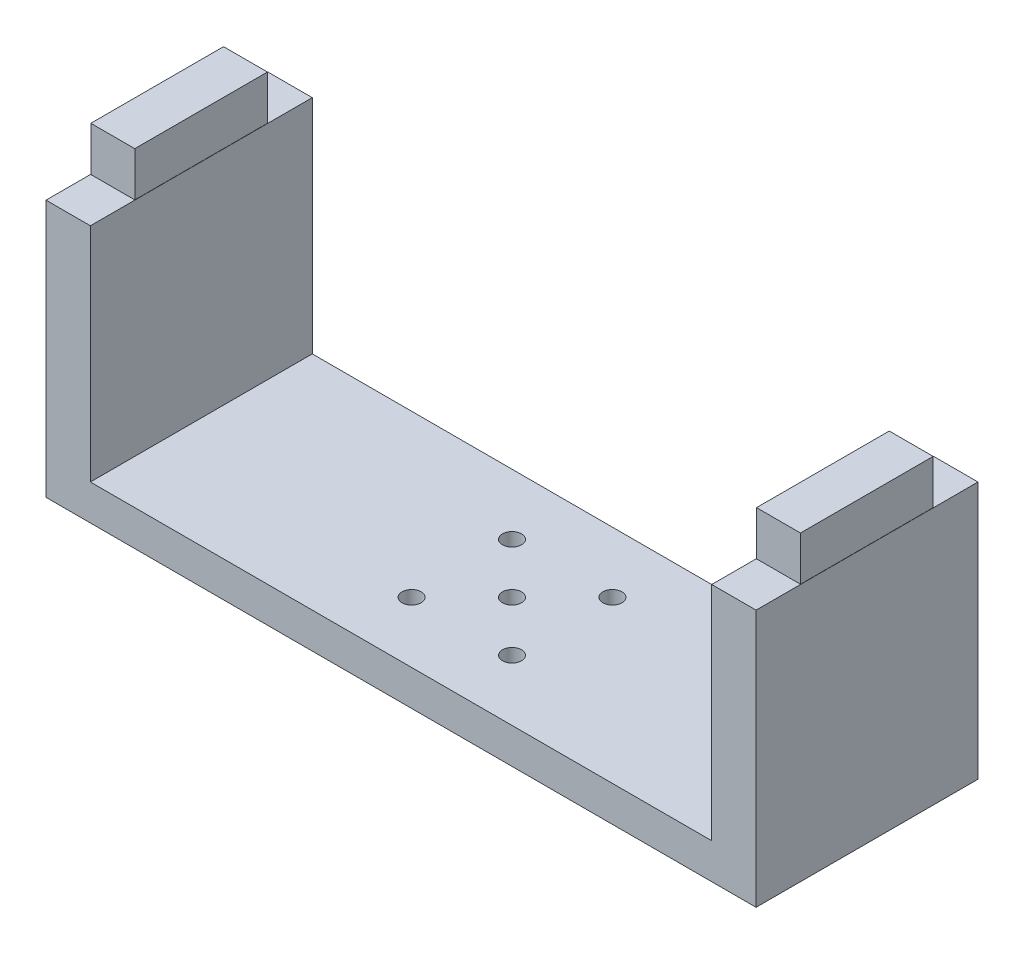
SolidWorks part; units mm, degrees
ref_plane "Front Plane" through (0, 0, 0) normal (0, 0, 1) x (1, 0, 0)
ref_plane "Top Plane" through (0, 0, 0) normal (0, 1, 0) x (1, 0, 0)
ref_plane "Right Plane" through (0, 0, 0) normal (1, 0, 0) x (0, 0, -1)
sketch "Sketch1" plane through (0, 0, 0) normal (0, 1, 0) x (1, 0, 0)
  line L1 (80, -25) -> (-80, -25)
  line L2 (80, -25) -> (80, 25)
  line L3 (80, 25) -> (-80, 25)
  line L4 (-80, -25) -> (-80, 25)
  line L5 (80, -25) -> (-80, 25) construction
  line L6 (80, 25) -> (-80, -25) construction
  point P0 (0, 0)
  dimension "D1" = 160
  dimension "D2" = 50
extrude "Boss-Extrude1" add sketch "Sketch1" along normal blind 8
sketch "Sketch2" plane through (0, 8, 0) normal (0, 1, 0) x (1, 0, 0)
  line L0 (0, 25) -> (0, -25) construction
  line L1 (80, 25) -> (-80, 25) construction
  line L2 (-80, -25) -> (80, -25) construction
  line L3 (-80, 25) -> (-80, -25) construction
  line L4 (-80, 25) -> (-70, 25)
  line L5 (-80, 25) -> (-80, -25)
  line L6 (-80, -25) -> (-70, -25)
  line L7 (-70, 25) -> (-70, -25)
  line L8 (80, -25) -> (70, -25)
  line L9 (70, 25) -> (70, -25)
  line L10 (80, 25) -> (70, 25)
  line L11 (80, 25) -> (80, -25)
  dimension "D1" = 50
  dimension "D2" = 10
extrude "Boss-Extrude2" add sketch "Sketch2" along normal blind 50
sketch "Sketch3" plane through (0, 58, 0) normal (0, 1, 0) x (1, 0, 0)
  line L0 (0, -25) -> (0, 25) construction
  line L1 (-70, -25) -> (70, -25) construction
  line L2 (70, 25) -> (-70, 25) construction
  line L4 (-70.05, -14.95) -> (-79.95, -14.95)
  line L5 (-70.05, -14.95) -> (-70.05, 14.95)
  line L6 (-70.05, 14.95) -> (-79.95, 14.95)
  line L7 (-79.95, -14.95) -> (-79.95, 14.95)
  line L10 (70.05, 14.95) -> (79.95, 14.95)
  line L11 (79.95, -14.95) -> (79.95, 14.95)
  line L12 (70.05, -14.95) -> (79.95, -14.95)
  line L13 (70.05, -14.95) -> (70.05, 14.95)
  line L14 (-70.05, 0) -> (-79.95, 0) construction
  line L16 (-70, 25) -> (-80, 25) construction
  line L21 (-75, -14.95) -> (-75, 14.95) construction
  line L25 (-70, -25) -> (-70, 25) construction
  dimension "D1" = 29.9
  dimension "D2" = 25
  dimension "D3" = 9.9
  dimension "D4" = 5
extrude "Boss-Extrude3" add sketch "Sketch3" along normal blind 10
sketch "Sketch4" plane through (0, 0, 0) normal (0, -1, 0) x (1, 0, 0)
  line L0 (-80, 25) -> (80, 25) construction
  line L1 (25, -25) -> (-25, -25) construction
  line L2 (25, -25) -> (25, 25) construction
  line L3 (25, 25) -> (-25, 25) construction
  line L4 (-25, -25) -> (-25, 25) construction
  line L5 (25, -25) -> (-25, 25) construction
  line L6 (25, 25) -> (-25, -25) construction
  circle A0 centre (0, 0) radius 2.15
  circle A1 centre (-11.3137, 11.3137) radius 2.15
  circle A2 centre (11.3137, 11.3137) radius 2.15
  circle A3 centre (11.3137, -11.3137) radius 2.15
  circle A4 centre (-11.3137, -11.3137) radius 2.15
  point P20 (0, 0)
  dimension "D1" = 4.3
  dimension "D3" = 4.3
  dimension "D4" = 16
  dimension "D2" = 50
  dimension "D5" = 4
extrude "Cut-Extrude1" cut sketch "Sketch4" against normal up to next
